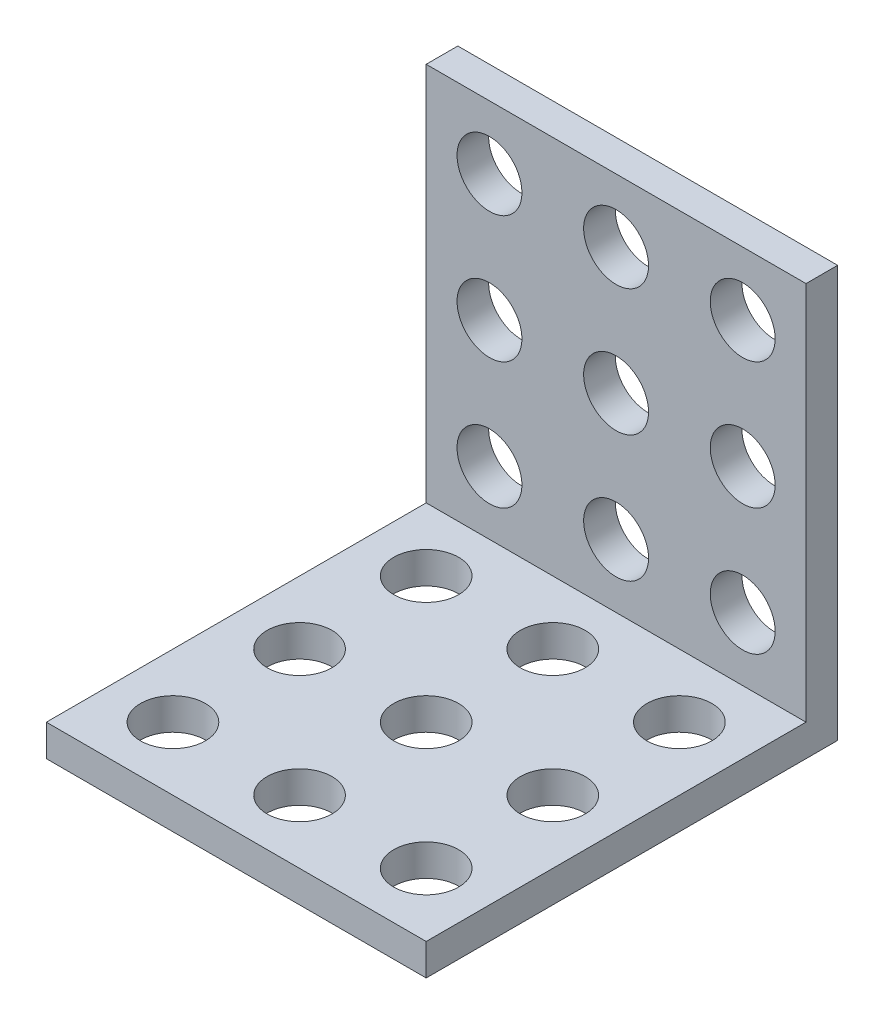
SolidWorks part; units mm, degrees
material "6061-O (SS)"
ref_plane "Front Plane" through (0, 0, 0) normal (0, 0, 1) x (1, 0, 0)
ref_plane "Top Plane" through (0, 0, 0) normal (0, 1, 0) x (1, 0, 0)
ref_plane "Right Plane" through (0, 0, 0) normal (1, 0, 0) x (0, 0, -1)
sketch "Sketch1" plane through (0, 0, 0) normal (1, 0, 0) x (0, 0, -1)
  line L0 (0, 0) -> (0, 26)
  line L1 (0, 26) -> (-2, 26)
  line L2 (-2, 26) -> (-2, 2)
  line L3 (-2, 2) -> (-26, 2)
  line L4 (-26, 2) -> (-26, 0)
  line L5 (-26, 0) -> (0, 0)
  dimension "D1" = 2
  dimension "D2" = 26
extrude "Boss-Extrude1" add sketch "Sketch1" along normal mid plane 24
sketch "Sketch3" plane through (0, 0, 2) normal (0, 0, 1) x (1, 0, 0)
  line L0 (0, 26) -> (0, 2) construction
  line L1 (12, 26) -> (-12, 26) construction
  line L2 (12, 2) -> (-12, 2) construction
  circle A0 centre (-8, 22) radius 2.05
  circle A1 centre (0, 22) radius 2.05
  circle A2 centre (8, 22) radius 2.05
  circle A3 centre (0, 14) radius 2.05
  circle A4 centre (8, 14) radius 2.05
  circle A5 centre (0, 6) radius 2.05
  circle A6 centre (8, 6) radius 2.05
  circle A7 centre (-8, 14) radius 2.05
  circle A8 centre (-8, 6) radius 2.05
  point P23 (0, 0)
  point P24 (0, 0)
  point P25 (0, 2)
  point P28 (8, 22)
  point P29 (0, 0)
  point P30 (0, 0)
  dimension "D3" = 8
  dimension "D4" = 8
  dimension "D5" = 4.1
  dimension "D1" = 3
  dimension "D2" = 3
extrude "Cut-Extrude1" cut sketch "Sketch3" against normal through all both and the other way through all
sketch "Sketch4" plane through (0, 2, 0) normal (0, 1, 0) x (1, 0, 0)
  line L0 (0, -2) -> (0, -26) construction
  line L1 (12, -2) -> (-12, -2) construction
  line L2 (12, -26) -> (-12, -26) construction
  circle A0 centre (-8, -22) radius 2.05
  circle A1 centre (0, -22) radius 2.05
  circle A2 centre (8, -22) radius 2.05
  circle A3 centre (0, -14) radius 2.05
  circle A4 centre (8, -14) radius 2.05
  circle A5 centre (0, -6) radius 2.05
  circle A6 centre (8, -6) radius 2.05
  circle A7 centre (-8, -14) radius 2.05
  circle A8 centre (-8, -6) radius 2.05
  point P8 (-8.6948, -12.9104)
  point P9 (0, 0)
  point P26 (0, 0)
  dimension "D3" = 8
  dimension "D4" = 8
  dimension "D5" = 4.1
  dimension "D1" = 3
  dimension "D2" = 3
extrude "Cut-Extrude2" cut sketch "Sketch4" against normal through all
